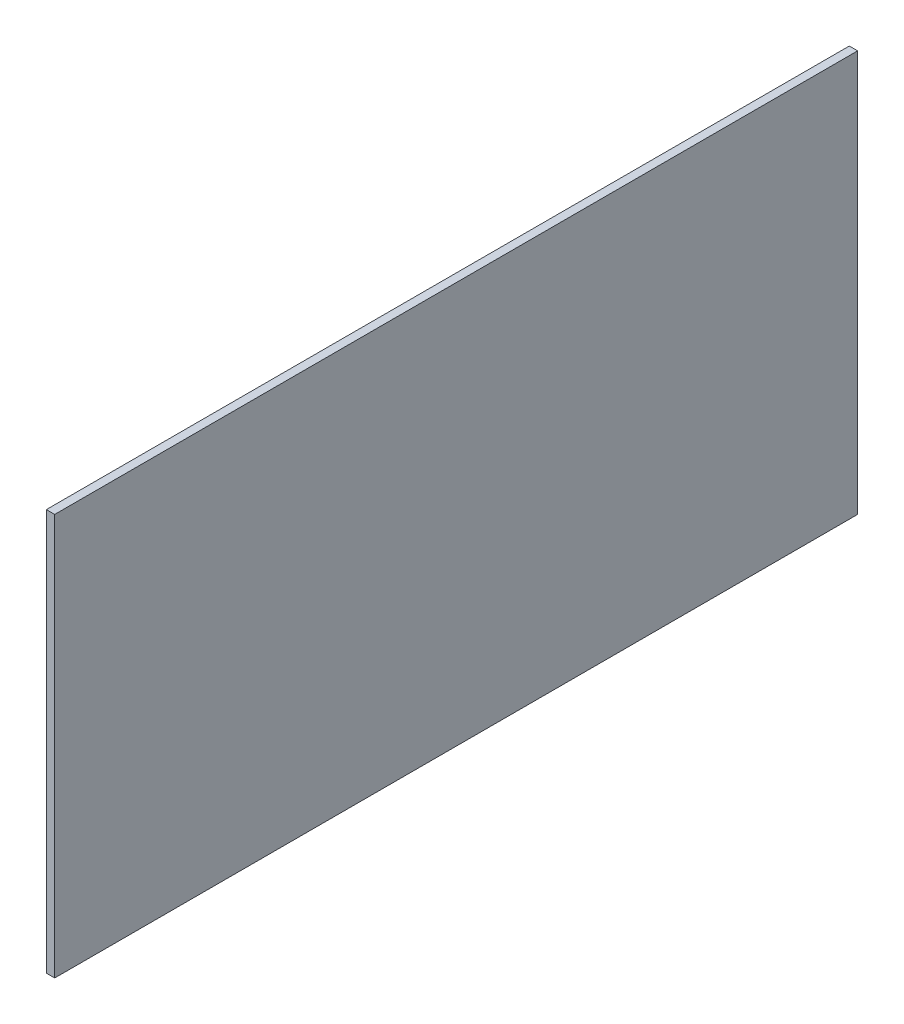
SolidWorks part; units mm, degrees
material "Polybutadiene (PB)"
ref_plane "Front Plane" through (0, 0, 0) normal (0, 0, 1) x (1, 0, 0)
ref_plane "Top Plane" through (0, 0, 0) normal (0, 1, 0) x (1, 0, 0)
ref_plane "Right Plane" through (0, 0, 0) normal (1, 0, 0) x (0, 0, -1)
sketch "Sketch1" plane through (0, 0, 0) normal (1, 0, 0) x (0, 0, -1)
  line L1 (-76.2, -38.1) -> (76.2, -38.1)
  line L2 (-76.2, -38.1) -> (-76.2, 38.1)
  line L3 (-76.2, 38.1) -> (76.2, 38.1)
  line L4 (76.2, -38.1) -> (76.2, 38.1)
  line L5 (-76.2, -38.1) -> (76.2, 38.1) construction
  line L6 (-76.2, 38.1) -> (76.2, -38.1) construction
  point P0 (0, 0)
  dimension "D1" = 152.4
  dimension "D2" = 76.2
extrude "Boss-Extrude1" add sketch "Sketch1" along normal blind 1.5875
equation "\"D1@Sketch1\"=6in"
equation "\"D2@Sketch1\"=3in"
equation "\"D1@Boss-Extrude1\"=1in/16"
